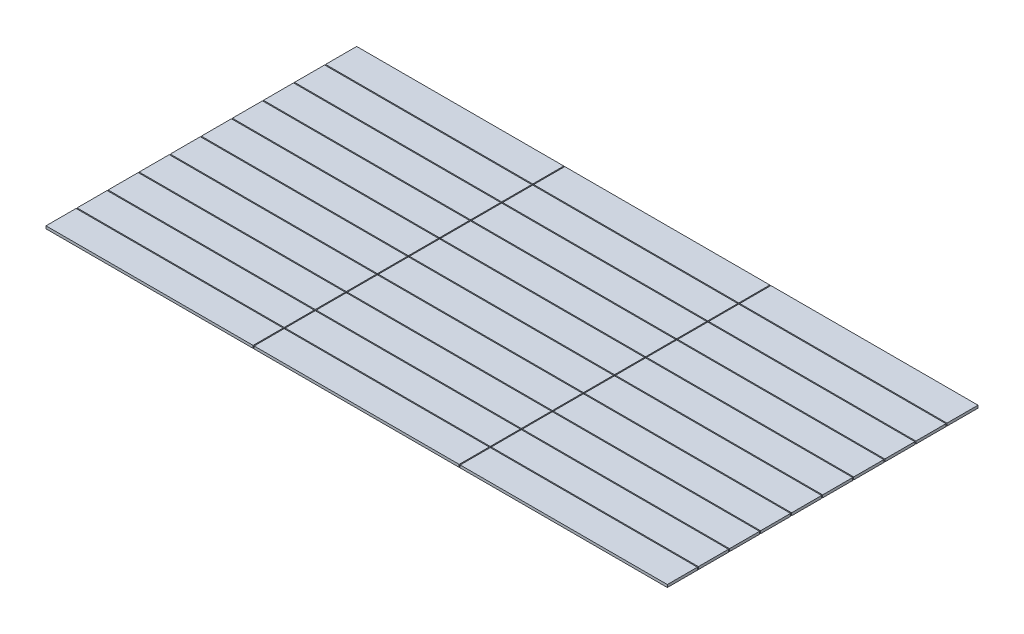
SolidWorks part; units mm, degrees
ref_plane "前视基准面" through (0, 0, 0) normal (0, 0, 1) x (1, 0, 0)
ref_plane "上视基准面" through (0, 0, 0) normal (0, 1, 0) x (1, 0, 0)
ref_plane "右视基准面" through (0, 0, 0) normal (1, 0, 0) x (0, 0, -1)
sketch "草图2" plane through (0, 0, 0) normal (0, 1, 0) x (1, 0, 0)
  line L1 (0, 0) -> (6000, 0)
  line L2 (0, 0) -> (0, 3000)
  line L3 (0, 3000) -> (6000, 3000)
  line L4 (6000, 0) -> (6000, 3000)
  dimension "D1" = 6000
  dimension "D2" = 3000
extrude "凸台-拉伸1" add sketch "草图2" along normal blind 25.4
sketch "草图3" plane through (0, 25.4, 0) normal (0, 1, 0) x (1, 0, 0)
  line L0 (0, 3000) -> (0, 0) construction
  line L1 (0, 2700) -> (6000, 2700)
  line L2 (0, 2700) -> (0, 2690)
  line L3 (0, 2690) -> (6000, 2690)
  line L4 (6000, 2700) -> (6000, 2690)
  line L5 (6000, 0) -> (6000, 3000) construction
  line L6 (6000, 3000) -> (0, 3000) construction
  line L7 (0, 2400) -> (6000, 2400)
  line L8 (6000, 2400) -> (6000, 2390)
  line L9 (0, 2390) -> (6000, 2390)
  line L10 (0, 2400) -> (0, 2390)
  line L11 (0, 2090) -> (6000, 2090)
  line L12 (0, 1800) -> (6000, 1800)
  line L13 (6000, 2100) -> (6000, 2090)
  line L14 (0, 1790) -> (6000, 1790)
  line L15 (0, 2100) -> (0, 2090)
  line L16 (0, 1800) -> (0, 1790)
  line L17 (0, 2100) -> (6000, 2100)
  line L18 (6000, 1800) -> (6000, 1790)
  line L19 (6000, 1500) -> (6000, 1490)
  line L20 (0, 890) -> (6000, 890)
  line L21 (6000, 1200) -> (6000, 1190)
  line L22 (0, 1190) -> (6000, 1190)
  line L23 (6000, 900) -> (6000, 890)
  line L24 (6000, 600) -> (6000, 590)
  line L25 (0, 900) -> (6000, 900)
  line L26 (0, 1200) -> (0, 1190)
  line L27 (0, 600) -> (6000, 600)
  line L28 (0, 1200) -> (6000, 1200)
  line L29 (0, 1490) -> (6000, 1490)
  line L30 (0, 900) -> (0, 890)
  line L31 (0, 600) -> (0, 590)
  line L32 (0, 1500) -> (6000, 1500)
  line L33 (0, 1500) -> (0, 1490)
  line L34 (0, 590) -> (6000, 590)
  line L35 (0, 290) -> (6000, 290)
  line L36 (0, 300) -> (6000, 300)
  line L37 (0, 300) -> (0, 290)
  line L38 (6000, 300) -> (6000, 290)
  dimension "D1" = 300
  dimension "D2" = 310
  dimension "D3" = 310
  dimension "D4" = 10
  dimension "D5" = 300
  dimension "D6" = 10
  dimension "D7" = 6000
  dimension "D8" = 6000
  dimension "D9" = 10
extrude "切除-拉伸1" cut sketch "草图3" against normal through all
sketch "草图4" plane through (0, 25.4, 0) normal (0, 1, 0) x (1, 0, 0)
  line L0 (6000, 3000) -> (0, 3000) construction
  line L1 (2000, 3000) -> (2010, 3000)
  line L2 (2000, 3000) -> (2000, 0)
  line L3 (2000, 0) -> (2010, 0)
  line L4 (2010, 3000) -> (2010, 0)
  line L5 (0, 0) -> (6000, 0) construction
  line L6 (0, 2090) -> (0, 1800) construction
  line L7 (3990, 3000) -> (4000, 3000)
  line L8 (3990, 3000) -> (3990, 0)
  line L9 (3990, 0) -> (4000, 0)
  line L10 (4000, 3000) -> (4000, 0)
  line L11 (6000, 1800) -> (6000, 2090) construction
  dimension "D1" = 10
  dimension "D2" = 10
  dimension "D3" = 2000
  dimension "D4" = 2000
extrude "切除-拉伸2" cut sketch "草图4" against normal blind 25.4
